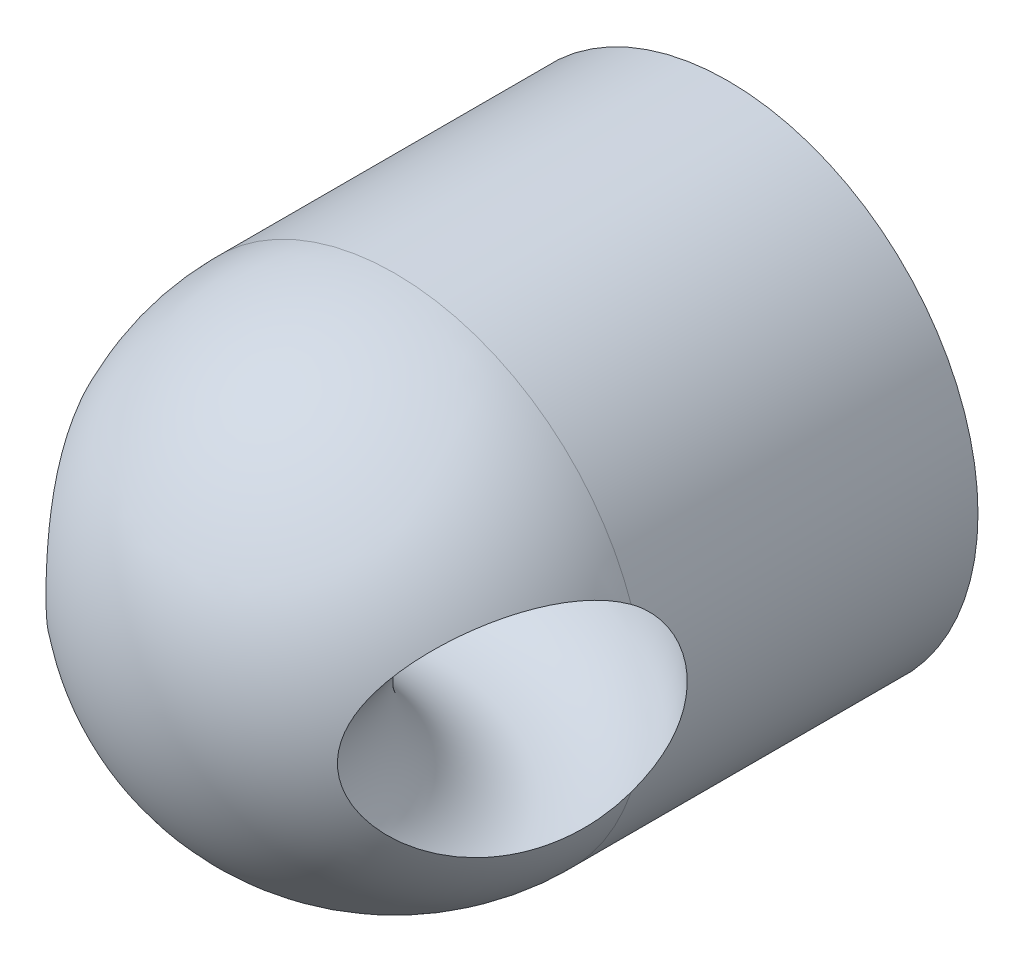
SolidWorks part; units mm, degrees
ref_plane "Front Plane" through (0, 0, 0) normal (0, 0, 1) x (1, 0, 0)
ref_plane "Top Plane" through (0, 0, 0) normal (0, 1, 0) x (1, 0, 0)
ref_plane "Right Plane" through (0, 0, 0) normal (1, 0, 0) x (0, 0, -1)
ref_axis "Axis3" through (0, 0, 10.5) along (0, 0, -1)
sketch "Sketch1" plane through (0, 0, 0) normal (0, 0, 1) x (1, 0, 0)
  circle A0 centre (0, 0) radius 6
  circle A1 centre (0, 0) radius 1.25
  dimension "D1" = 12
  dimension "D2" = 2.5
extrude "Main" add sketch "Sketch1" along normal blind 8
sketch "Sketch3" plane through (0, 0, 0) normal (1, 0, 0) x (0, 0, -1)
  line L0 (-8, 6) -> (-8, -6) construction
  line L1 (-10.5, 0) -> (0.5, 0) construction
  line L2 (-8, 0) -> (-14, 0)
  line L5 (-8, 0) -> (-8, -6)
  arc A1 (-14, 0) -> (-8, -6) centre (-8, 0) ccw
  point P1 (-8, -0.0763)
  point P2 (-8.1247, 0)
  dimension "D1" = 6
revolve "TopMain" add sketch "Sketch3" angle 360 about axis through (0, 0, 10.5) along (0, 0, -1)
ref_plane "Plane1" through (0, 0, 13) normal (0, 0, 1) x (1, 0, 0)
ref_axis "Axis4" through (0, 6.6, 13) along (0, -1, 0)
sketch "Sketch4" plane through (0, 0, 0) normal (1, 0, 0) x (0, 0, -1)
  line L2 (0, -6) -> (0, 6) construction
  line L3 (-10.5, 0) -> (0.5, 0) construction
  circle A0 centre (-7, 0) radius 2.5
  point P2 (-8, 0.5412)
  point P3 (-7.0186, 0)
  point P4 (-5.7356, 0)
  point P7 (-7, 0)
  dimension "D1" = 5
  dimension "D2" = 7
revolve "HookHole" cut sketch "Sketch4" angle 360 about axis through (0, 6.6, 13) along (0, -1, 0)
